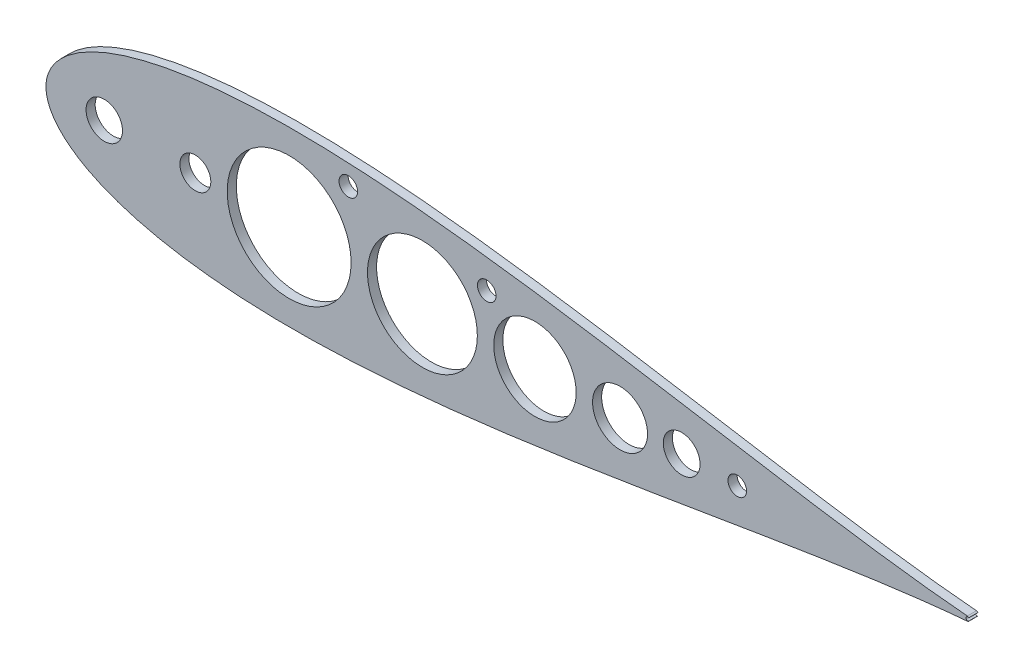
SolidWorks part; units mm, degrees
material "Balsa"
ref_plane "Front Plane" through (0, 0, 0) normal (0, 0, 1) x (1, 0, 0)
ref_plane "Top Plane" through (0, 0, 0) normal (0, 1, 0) x (1, 0, 0)
ref_plane "Right Plane" through (0, 0, 0) normal (1, 0, 0) x (0, 0, -1)
curve "Curve4"
  spline degree 3 poles (100, 0, 0) (99.8498, 0.0023, 0) (99.4759, 0.008, 0) (99.1023, 0.0238, 0) (98.8789, 0.0332, 0) knots 0 0 0 0 0.401829 1 1 1 1
curve "Curve5"
  spline degree 3 poles (99.3714, -0.0082, 0) (100.2526, 0, 0) (99.3714, 0.0082, 0) (98.8504, 0.035, 0) (97.904, 0.0811, 0) (96.8285, 0.1543, 0) (95.5159, 0.2583, 0) (94.013, 0.3972, 0) (92.313, 0.574, 0) (90.4281, 0.791, 0) (88.3655, 1.0495, 0) (86.1348, 1.3497, 0) (83.7456, 1.691, 0) (81.2082, 2.0715, 0) (78.5335, 2.4886, 0) (75.7326, 2.9386, 0) (72.8172, 3.4168, 0) (69.799, 3.9177, 0) (66.6904, 4.435, 0) (63.5039, 4.9616, 0) (60.2521, 5.4899, 0) (56.948, 6.0119, 0) (53.6049, 6.519, 0) (50.2363, 7.0024, 0) (46.8558, 7.4534, 0) (43.4774, 7.8632, 0) (40.1152, 8.2232, 0) (36.7837, 8.5249, 0) (33.4975, 8.7606, 0) (30.2716, 8.923, 0) (27.1211, 9.0055, 0) (24.0614, 9.0025, 0) (21.108, 8.909, 0) (18.277, 8.7213, 0) (15.5843, 8.4369, 0) (13.0466, 8.0543, 0) (10.6806, 7.5735, 0) (8.5039, 6.996, 0) (6.5349, 6.3253, 0) (4.7933, 5.5673, 0) (3.3001, 4.7321, 0) (2.0777, 3.8366, 0) (1.1467, 2.91, 0) (0.5165, 2.0014, 0) (0.165, 1.1816, 0) (0.0231, 0.524, 0) (-0.0093, 0, 0) (0.0231, -0.524, 0) (0.165, -1.1816, 0) (0.5165, -2.0014, 0) (1.1467, -2.91, 0) (2.0777, -3.8366, 0) (3.3001, -4.7321, 0) (4.7933, -5.5673, 0) (6.5349, -6.3253, 0) (8.5039, -6.996, 0) (10.6806, -7.5735, 0) (13.0466, -8.0543, 0) (15.5843, -8.4369, 0) (18.277, -8.7213, 0) (21.108, -8.909, 0) (24.0614, -9.0025, 0) (27.1211, -9.0055, 0) (30.2716, -8.923, 0) (33.4975, -8.7606, 0) (36.7837, -8.5249, 0) (40.1152, -8.2232, 0) (43.4774, -7.8632, 0) (46.8558, -7.4534, 0) (50.2363, -7.0024, 0) (53.6049, -6.519, 0) (56.948, -6.0119, 0) (60.2521, -5.4899, 0) (63.5039, -4.9616, 0) (66.6904, -4.435, 0) (69.799, -3.9177, 0) (72.8172, -3.4168, 0) (75.7326, -2.9386, 0) (78.5335, -2.4886, 0) (81.2082, -2.0715, 0) (83.7456, -1.691, 0) (86.1348, -1.3497, 0) (88.3655, -1.0495, 0) (90.4281, -0.791, 0) (92.313, -0.574, 0) (94.013, -0.3972, 0) (95.5159, -0.2583, 0) (96.8285, -0.1543, 0) (97.904, -0.0811, 0) (98.8504, -0.035, 0) (99.3714, -0.0082, 0) (100.2526, 0, 0) (99.3714, 0.0082, 0) knots -0.009667 -0.005395 -0.002168 0 0.002168 0.005395 0.009667 0.014967 0.021271 0.028553 0.036781 0.04592 0.055932 0.066773 0.078397 0.090755 0.103793 0.117456 0.131686 0.146422 0.1616 0.177156 0.193024 0.209135 0.225421 0.241812 0.258238 0.274629 0.290914 0.307025 0.322893 0.338448 0.353626 0.368361 0.38259 0.396253 0.40929 0.421647 0.43327 0.444109 0.454119 0.463255 0.471479 0.478755 0.485052 0.490344 0.49461 0.497833 0.5 0.502167 0.50539 0.509656 0.514948 0.521245 0.528521 0.536745 0.545881 0.555891 0.56673 0.578353 0.59071 0.603747 0.61741 0.631639 0.646374 0.661552 0.677107 0.692975 0.709086 0.725371 0.741762 0.758188 0.774579 0.790865 0.806976 0.822844 0.8384 0.853578 0.868314 0.882544 0.896207 0.909245 0.921603 0.933227 0.944068 0.95408 0.963219 0.971447 0.978729 0.985033 0.990333 0.994605 0.997832 1 1.002168 1.005395 1.009667 periodic
sketch "Sketch2" plane through (0, 0, 0) normal (0, 0, 1) x (1, 0, 0)
  line L0 (100, 0) -> (0, 0) construction
  line L2 (93.345, 0) -> (114.935, 0) construction
  line L4 (643.5991, 0) -> (643.5991, -1.016)
  line L9 (0, 0) -> (643.9668, 0)
  line L13 (460.661, 0) -> (473.361, 0)
  circle A0 centre (104.14, 0) radius 10.795 construction
  arc A2 (641.5671, 0) -> (644.1071, 0) centre (642.8371, 0) ccw
  circle A4 centre (104.14, 0) radius 10.795
  circle A9 centre (40.64, 0) radius 12.7
  circle A14 centre (642.3793, 0) radius 1.5875 construction
  arc A15 (642.5108, -1.582) -> (642.5108, 1.582) centre (642.3793, 0) ccw
  spline S2 degree 3 poles (666.3448, -0.0547) (672.2538, 0) (666.3448, 0.0547) (662.8509, 0.2344) (656.505, 0.5436) (649.293, 1.0348) (640.4916, 1.7319) (630.4138, 2.6634) (619.0141, 3.8493) (606.375, 5.3044) (592.5439, 7.0376) (577.5855, 9.0506) (561.5643, 11.3389) (544.5497, 13.8907) (526.6141, 16.6877) (507.8326, 19.7051) (488.2827, 22.9117) (468.0444, 26.2704) (447.1994, 29.739) (425.8316, 33.2703) (404.0263, 36.8132) (381.8707, 40.3133) (359.4533, 43.7135) (336.8645, 46.9554) (314.1962, 49.9798) (291.5418, 52.7277) (268.9963, 55.1412) (246.6566, 57.1646) (224.6209, 58.7452) (202.9892, 59.8341) (181.8631, 60.3875) (161.3458, 60.367) (141.542, 59.7399) (122.5581, 58.4818) (104.5023, 56.5743) (87.485, 54.0089) (71.6197, 50.7848) (57.0237, 46.9125) (43.8205, 42.415) (32.1416, 37.3322) (22.1291, 31.7315) (13.9324, 25.7264) (7.6896, 19.5132) (3.4631, 13.4204) (1.1063, 7.9234) (0.1546, 3.5138) (-0.0622, 0) (0.1546, -3.5138) (1.1063, -7.9234) (3.4631, -13.4204) (7.6896, -19.5132) (13.9324, -25.7264) (22.1291, -31.7315) (32.1416, -37.3322) (43.8205, -42.415) (57.0237, -46.9125) (71.6197, -50.7848) (87.485, -54.0089) (104.5023, -56.5743) (122.5581, -58.4818) (141.542, -59.7399) (161.3458, -60.367) (181.8631, -60.3875) (202.9892, -59.8341) (224.6209, -58.7452) (246.6566, -57.1646) (268.9963, -55.1412) (291.5418, -52.7277) (314.1962, -49.9798) (336.8645, -46.9554) (359.4533, -43.7135) (381.8707, -40.3133) (404.0263, -36.8132) (425.8316, -33.2703) (447.1994, -29.739) (468.0444, -26.2704) (488.2827, -22.9117) (507.8326, -19.7051) (526.6141, -16.6877) (544.5497, -13.8907) (561.5643, -11.3389) (577.5855, -9.0506) (592.5439, -7.0376) (606.375, -5.3044) (619.0141, -3.8493) (630.4138, -2.6634) (640.4916, -1.7319) (649.293, -1.0348) (656.505, -0.5436) (662.8509, -0.2344) (666.3448, -0.0547) (672.2538, 0) (666.3448, 0.0547) knots -0.009667 -0.005395 -0.002168 0 0.002168 0.005395 0.009667 0.014967 0.021271 0.028553 0.036781 0.04592 0.055932 0.066773 0.078397 0.090755 0.103793 0.117456 0.131686 0.146422 0.1616 0.177156 0.193024 0.209135 0.225421 0.241812 0.258238 0.274629 0.290914 0.307025 0.322893 0.338448 0.353626 0.368361 0.38259 0.396253 0.40929 0.421647 0.43327 0.444109 0.454119 0.463255 0.471479 0.478755 0.485052 0.490344 0.49461 0.497833 0.5 0.502167 0.50539 0.509656 0.514948 0.521245 0.528521 0.536745 0.545881 0.555891 0.56673 0.578353 0.59071 0.603747 0.61741 0.631639 0.646374 0.661552 0.677107 0.692975 0.709086 0.725371 0.741762 0.758188 0.774579 0.790865 0.806976 0.822844 0.8384 0.853578 0.868314 0.882544 0.896207 0.909245 0.921603 0.933227 0.944068 0.95408 0.963219 0.971447 0.978729 0.985033 0.990333 0.994605 0.997832 1 1.002168 1.005395 1.009667 only from (670.56, 0) to (670.56, 0)
  point P2 (167.64, 0)
  dimension "D2" = 21.59
  dimension "D8" = 25.4
  dimension "D10" = 3.175
  dimension "D1" = 167.64
  dimension "D6" = 63.5
  dimension "D9" = 63.5
  dimension "D3" = 1.016
  dimension "D4" = 1.27
extrude "Boss-Extrude1" add sketch "Sketch2" along normal blind 6.35
sketch "Sketch3" plane through (0, 0, 6.35) normal (0, 0, 1) x (1, 0, 0)
  line L0 (84.14, -12.7) -> (62.637, -12.7) construction
  line L1 (430.4749, -1041.2705) -> (430.4749, 48958.7295) construction
  line L2 (114.935, 0) -> (641.5671, 0) construction
  line L3 (27.94, 0) -> (0, 0)
  line L4 (641.5671, 0) -> (114.935, 0)
  line L5 (93.345, 0) -> (53.34, 0)
  line L6 (27.94, 0) -> (0, 0)
  line L7 (212.768, -1000) -> (212.768, 49000) construction
  line L8 (93.345, 0) -> (53.34, 0)
  line L9 (224.198, -1000) -> (224.198, 49000) construction
  line L10 (300.8092, -1000) -> (300.8092, 49000) construction
  line L11 (312.2392, -1000) -> (312.2392, 49000) construction
  line L12 (369.7207, -1000) -> (369.7207, 49000) construction
  line L13 (93.345, -17.145) -> (65.0689, -17.145) construction
  line L14 (419.5047, -1000) -> (419.5047, 49000) construction
  line L15 (126.365, -1000) -> (126.365, 49000) construction
  line L16 (381.1507, -1000) -> (381.1507, 49000) construction
  line L17 (52.7726, -27.2676) -> (52.7726, -27.2676) construction
  arc A0 (36.4352, -25.0495) -> (62.637, -12.7) centre (40.64, 0) ccw construction
  circle A2 centre (169.5665, 0) radius 43.2015
  arc A3 (642.5108, -1.582) -> (643.5991, -1.016) centre (642.3793, 0) ccw
  arc A4 (93.345, 0) -> (114.935, 0) centre (104.14, 0) ccw
  arc A5 (27.94, 0) -> (53.34, 0) centre (40.64, 0) ccw
  arc A6 (642.5108, -1.582) -> (643.5991, -1.016) centre (642.3793, 0) ccw
  circle A7 centre (262.5036, 0) radius 38.3056
  arc A8 (27.94, 0) -> (53.34, 0) centre (40.64, 0) ccw
  circle A9 centre (340.9799, 0) radius 28.7408
  circle A10 centre (400.3277, 0) radius 19.177
  circle A11 centre (443.3019, 0) radius 12.827
  circle A12 centre (482.0825, 0) radius 6.477
  arc A13 (52.7726, -27.2676) -> (65.0689, -17.145) centre (40.64, 0) ccw construction
  arc A14 (638.2053, 15.2585) -> (638.2053, 15.2585) centre (638.2053, 15.2585) ccw construction
  arc A18 (641.5671, 0) -> (643.5991, -1.016) centre (642.8371, 0) ccw
  arc A19 (641.5671, 0) -> (643.5991, -1.016) centre (642.8371, 0) ccw
  spline S1 degree 3 poles (1488.1541, -2580.0534) (314.1987, 184.2642) (-15.4092, 68.5977) (1.1063, -7.9234) (3.4631, -13.4204) (7.6896, -19.5132) (13.9324, -25.7264) (22.1291, -31.7315) (32.1416, -37.3322) (43.8205, -42.415) (57.0237, -46.9125) (71.6197, -50.7848) (87.485, -54.0089) (104.5023, -56.5743) (122.5581, -58.4818) (141.542, -59.7399) (161.3458, -60.367) (181.8631, -60.3875) (202.9892, -59.8341) (224.6209, -58.7452) (246.6566, -57.1646) (268.9963, -55.1412) (291.5418, -52.7277) (314.1962, -49.9798) (336.8645, -46.9554) (359.4533, -43.7135) (381.8707, -40.3133) (404.0263, -36.8132) (425.8316, -33.2703) (447.1994, -29.739) (468.0444, -26.2704) (488.2827, -22.9117) (507.8326, -19.7051) (526.6141, -16.6877) (544.5497, -13.8907) (561.5643, -11.3389) (577.5855, -9.0506) (592.5439, -7.0376) (606.375, -5.3044) (619.0141, -3.8493) (630.4138, -2.6634) (754.7119, 8.8252) (895.5191, -9.0089) (-2343.84, -283.812) knots 0.342093 0.342093 0.342093 0.342093 0.502167 0.50539 0.509656 0.514948 0.521245 0.528521 0.536745 0.545881 0.555891 0.56673 0.578353 0.59071 0.603747 0.61741 0.631639 0.646374 0.661552 0.677107 0.692975 0.709086 0.725371 0.741762 0.758188 0.774579 0.790865 0.806976 0.822844 0.8384 0.853578 0.868314 0.882544 0.896207 0.909245 0.921603 0.933227 0.944068 0.95408 0.963219 0.971447 0.978729 1.23227 1.23227 1.23227 1.23227 only from (0, 0) to (642.5108, -1.582)
  spline S2 degree 3 poles (0, 0) (0, -1.0075) (0.1546, -3.5138) (1.1063, -7.9234) (3.4631, -13.4204) (7.6896, -19.5132) (13.9324, -25.7264) (22.1291, -31.7315) (32.1416, -37.3322) (43.8205, -42.415) (57.0237, -46.9125) (71.6197, -50.7848) (87.485, -54.0089) (104.5023, -56.5743) (122.5581, -58.4818) (141.542, -59.7399) (161.3458, -60.367) (181.8631, -60.3875) (202.9892, -59.8341) (224.6209, -58.7452) (246.6566, -57.1646) (268.9963, -55.1412) (291.5418, -52.7277) (314.1962, -49.9798) (336.8645, -46.9554) (359.4533, -43.7135) (381.8707, -40.3133) (404.0263, -36.8132) (425.8316, -33.2703) (447.1994, -29.739) (468.0444, -26.2704) (488.2827, -22.9117) (507.8326, -19.7051) (526.6141, -16.6877) (544.5497, -13.8907) (561.5643, -11.3389) (577.5855, -9.0506) (592.5439, -7.0376) (606.375, -5.3044) (619.0141, -3.8493) (630.4138, -2.6634) (638.0937, -1.9535) (641.9934, -1.6251) (642.5108, -1.582) knots 0.5 0.5 0.5 0.5 0.502167 0.50539 0.509656 0.514948 0.521245 0.528521 0.536745 0.545881 0.555891 0.56673 0.578353 0.59071 0.603747 0.61741 0.631639 0.646374 0.661552 0.677107 0.692975 0.709086 0.725371 0.741762 0.758188 0.774579 0.790865 0.806976 0.822844 0.8384 0.853578 0.868314 0.882544 0.896207 0.909245 0.921603 0.933227 0.944068 0.95408 0.963219 0.971447 0.978729 0.979843 0.979843 0.979843 0.979843
  spline S4 degree 1 poles (52.7726, -27.2676) (638.2053, 15.2585) knots 0 0 1 1 construction
  spline S5 degree 3 poles (52.7726, -27.2676) (54.098, -27.7509) (56.7529, -28.6784) (62.1794, -30.4243) (69.1006, -32.3953) (77.5892, -34.4571) (89.0862, -36.8389) (103.7331, -39.1926) (125.3657, -41.6037) (144.2709, -42.7116) (163.2853, -43.1964) (177.6693, -43.2555) (201.2447, -42.8023) (227.4371, -41.4675) (254.4928, -39.2877) (277.8401, -36.9937) (301.0423, -34.3583) (330.3789, -30.5811) (368.329, -25.1309) (404.83, -19.3409) (435.2358, -14.3425) (451.6826, -11.6119) (464.2574, -9.5208) (476.8398, -7.4307) (497.3171, -4.0443) (526.9629, 0.7645) (562.929, 6.2684) (594.1055, 10.5252) (616.0859, 13.0867) (628.694, 14.3901) (635.0364, 14.9826) (638.2053, 15.2585) knots 0.548481 0.548481 0.548481 0.548481 0.551835 0.555189 0.561898 0.568606 0.575315 0.588731 0.602148 0.62409 0.630798 0.644215 0.655815 0.682649 0.701659 0.715076 0.733763 0.752449 0.779283 0.816817 0.832298 0.845715 0.852722 0.859728 0.873145 0.897318 0.924152 0.950985 0.964402 0.971111 0.977819 0.977819 0.977819 0.977819 construction
  line M19 (641.5671, 0) -> (114.935, 0)
  dimension "D3" = 11.43
  dimension "D7" = 38.354
  dimension "D8" = 25.654
  dimension "D9" = 12.954
  dimension "D4" = 11.43
  dimension "D5" = 11.43
  dimension "D6" = 11.43
  dimension "D1" = 0
  dimension "D10" = 17.145
extrude "Cut-Extrude2" cut sketch "Sketch3" against normal through all both and the other way through all contours A2 M19 | A7 M19 | A9 M19 | A10 M19 | A11 M19 | A12 M19
mirror "Mirror1" about plane through (0, 0, 0) normal (0, 1, 0) of "Cut-Extrude2", "Boss-Extrude1"
sketch "Sketch4" plane through (0, 0, 6.35) normal (0, 0, 1) x (1, 0, 0)
  line L0 (104.14, 0) -> (642.8371, 0) construction
  circle A0 centre (210.82, 45.212) radius 6.477
  circle A1 centre (307.34, 30.48) radius 6.477
  point P0 (104.14, 0)
  dimension "D2" = 12.954
  dimension "D1" = 106.68
  dimension "D3" = 45.212
  dimension "D4" = 30.48
  dimension "D5" = 203.2
extrude "Cut-Extrude3" cut sketch "Sketch4" against normal through all
equation "\"0.5n\"=0"
equation "\"ROD DIAM\"= \"D2@Sketch2\""
